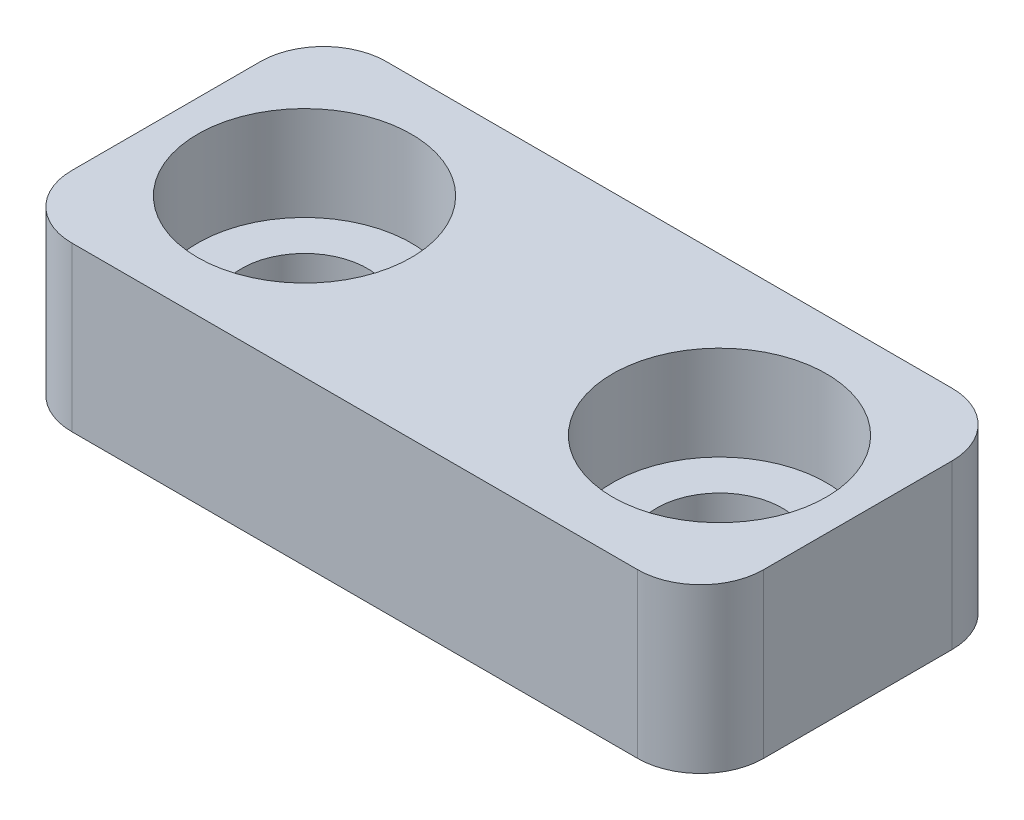
SolidWorks part; units mm, degrees
material "Custom Plastic"
ref_plane "Front Plane" through (0, 0, 0) normal (0, 0, 1) x (1, 0, 0)
ref_plane "Top Plane" through (0, 0, 0) normal (0, 1, 0) x (1, 0, 0)
ref_plane "Right Plane" through (0, 0, 0) normal (1, 0, 0) x (0, 0, -1)
sketch "Sketch1" plane through (0, 0, 0) normal (0, 1, 0) x (1, 0, 0)
  line L0 (-7.4485, 0) -> (7.8729, 0) construction
  line L1 (-5.5, -2.5) -> (5.5, -2.5)
  line L2 (-5.5, -2.5) -> (-5.5, 2.5)
  line L3 (-5.5, 2.5) -> (5.5, 2.5)
  line L4 (5.5, -2.5) -> (5.5, 2.5)
  line L5 (-5.5, -2.5) -> (5.5, 2.5) construction
  line L6 (-5.5, 2.5) -> (5.5, -2.5) construction
  circle A0 centre (-3.3, 0) radius 1
  circle A1 centre (3.3, 0) radius 1
  point P0 (0, 0)
  dimension "D5" = 2
  dimension "D6" = 2
  dimension "D1" = 11
  dimension "D2" = 5
  dimension "D3" = 2.2
  dimension "D4" = 2.2
extrude "Boss-Extrude1" add sketch "Sketch1" along normal blind 2.6
sketch "Sketch2" plane through (0, 2.6, 0) normal (0, 1, 0) x (1, 0, 0)
  circle A0 centre (-3.3, 0) radius 1.7
  circle A1 centre (3.3, 0) radius 1.7
  dimension "D1" = 3.4
  dimension "D2" = 3.4
extrude "Cut-Extrude1" cut sketch "Sketch2" against normal blind 1.5
fillet "Fillet1" radius 1 4 edges at (5.5, 1.3, 2.5) (5.5, 1.3, -2.5) (-5.5, 1.3, -2.5) (-5.5, 1.3, 2.5)
